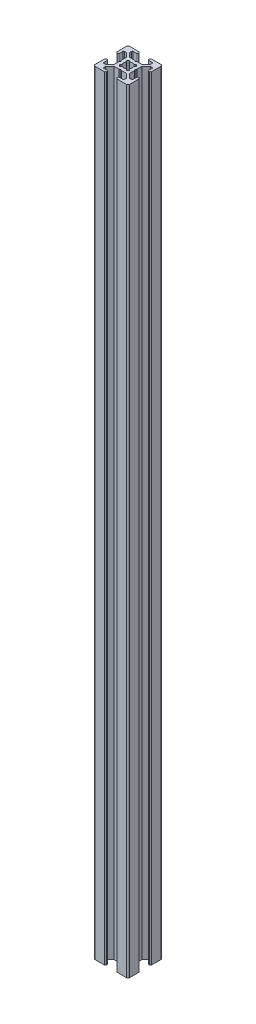
SolidWorks part; units mm, degrees
ref_plane "Front Plane" through (0, 0, 0) normal (0, 0, 1) x (1, 0, 0)
ref_plane "Top Plane" through (0, 0, 0) normal (0, 1, 0) x (1, 0, 0)
ref_plane "Right Plane" through (0, 0, 0) normal (1, 0, 0) x (0, 0, -1)
sketch "Sketch3" plane through (0, 0, 0) normal (0, 1, 0) x (1, 0, 0)
  line L0 (7, 20) -> (7, 18.5)
  line L1 (0, 0) -> (20, 0)
  line L2 (0, 0) -> (0, 20)
  line L3 (0, 20) -> (20, 20)
  line L4 (20, 0) -> (20, 20)
  line L5 (7, 18.5) -> (4, 18.5)
  line L6 (4, 18.5) -> (4, 17)
  line L7 (4, 17) -> (6.5, 14.5)
  line L8 (6.5, 14.5) -> (13.5, 14.5)
  line L9 (13.5, 14.5) -> (16, 17)
  line L10 (16, 17) -> (16, 18.5)
  line L11 (16, 18.5) -> (13, 18.5)
  line L12 (13, 18.5) -> (13, 20)
  line L13 (13, 20) -> (7, 20)
  line L14 (9.5, 14.5) -> (10, 14)
  line L15 (10, 14) -> (10.5, 14.5)
  line L16 (10.5, 14.5) -> (9.5, 14.5)
  line L17 (13, 19.5) -> (13, 20)
  line L18 (13.5, 20) -> (13, 20)
  line L19 (7, 19.5) -> (7, 20)
  line L20 (6.5, 20) -> (7, 20)
  line L21 (0, 13) -> (1.5, 13)
  line L22 (1.5, 13) -> (1.5, 16)
  line L23 (1.5, 16) -> (3, 16)
  line L24 (3, 16) -> (5.5, 13.5)
  line L25 (5.5, 13.5) -> (5.5, 6.5)
  line L26 (5.5, 6.5) -> (3, 4)
  line L27 (3, 4) -> (1.5, 4)
  line L28 (1.5, 4) -> (1.5, 7)
  line L29 (1.5, 7) -> (0, 7)
  line L30 (0, 7) -> (0, 13)
  line L31 (5.5, 10.5) -> (5.5, 9.5)
  line L32 (5.5, 9.5) -> (6, 10)
  line L33 (6, 10) -> (5.5, 10.5)
  line L34 (0.5, 13) -> (0, 13)
  line L35 (0, 13.5) -> (0, 13)
  line L36 (0, 6.5) -> (0, 7)
  line L37 (0.5, 7) -> (0, 7)
  line L38 (10, 20) -> (10, 0) construction
  line L39 (20, 10) -> (0, 10) construction
  line L40 (10, 6) -> (10.5, 5.5)
  line L41 (9.5, 5.5) -> (10, 6)
  line L42 (10.5, 5.5) -> (9.5, 5.5)
  line L43 (13.5, 0) -> (13, 0)
  line L44 (13, 0.5) -> (13, 0)
  line L45 (6.5, 0) -> (7, 0)
  line L46 (7, 0.5) -> (7, 0)
  line L47 (13, 1.5) -> (13, 0)
  line L48 (16, 1.5) -> (13, 1.5)
  line L49 (16, 3) -> (16, 1.5)
  line L50 (13.5, 5.5) -> (16, 3)
  line L51 (6.5, 5.5) -> (13.5, 5.5)
  line L52 (4, 3) -> (6.5, 5.5)
  line L53 (4, 1.5) -> (4, 3)
  line L54 (7, 1.5) -> (4, 1.5)
  line L55 (7, 0) -> (7, 1.5)
  line L56 (13, 0) -> (7, 0)
  line L57 (14.5, 9.5) -> (14, 10)
  line L58 (14.5, 10.5) -> (14.5, 9.5)
  line L59 (14, 10) -> (14.5, 10.5)
  line L60 (19.5, 7) -> (20, 7)
  line L61 (20, 6.5) -> (20, 7)
  line L62 (20, 13.5) -> (20, 13)
  line L63 (19.5, 13) -> (20, 13)
  line L64 (18.5, 7) -> (20, 7)
  line L65 (18.5, 4) -> (18.5, 7)
  line L66 (17, 4) -> (18.5, 4)
  line L67 (14.5, 6.5) -> (17, 4)
  line L68 (14.5, 13.5) -> (14.5, 6.5)
  line L69 (17, 16) -> (14.5, 13.5)
  line L70 (18.5, 16) -> (17, 16)
  line L71 (18.5, 13) -> (18.5, 16)
  line L72 (20, 13) -> (18.5, 13)
  line L73 (20, 7) -> (20, 13)
  arc A0 (13.5, 20) -> (13, 19.5) centre (13, 20) cw
  arc A1 (6.5, 20) -> (7, 19.5) centre (7, 20) ccw
  arc A2 (0.5, 13) -> (0, 13.5) centre (0, 13) ccw
  arc A3 (0.5, 7) -> (0, 6.5) centre (0, 7) cw
  arc A4 (13.5, 0) -> (13, 0.5) centre (13, 0) ccw
  arc A5 (6.5, 0) -> (7, 0.5) centre (7, 0) cw
  arc A6 (19.5, 7) -> (20, 6.5) centre (20, 7) ccw
  arc A7 (19.5, 13) -> (20, 13.5) centre (20, 13) cw
  point P7 (10, 14.5)
  point P16 (10, 20)
  point P26 (5.5, 10)
  point P35 (0, 10)
  dimension "D16" = 0.5
  dimension "D17" = 0.5
  dimension "D28" = 0.5
  dimension "D29" = 0.5
  dimension "D1" = 20
  dimension "D2" = 20
  dimension "D3" = 7
  dimension "D4" = 7
  dimension "D5" = 1.5
  dimension "D6" = 1.5
  dimension "D7" = 3
  dimension "D8" = 3
  dimension "D9" = 1.5
  dimension "D10" = 1.5
  dimension "D11" = 7
  dimension "D12" = 5.5
  dimension "D13" = 0.5
  dimension "D14" = 0.5
  dimension "D15" = 0.5
  dimension "D18" = 7
  dimension "D19" = 7
  dimension "D20" = 1.5
  dimension "D21" = 1.5
  dimension "D22" = 3
  dimension "D23" = 7
  dimension "D24" = 5.5
  dimension "D25" = 0.5
  dimension "D26" = 0.5
  dimension "D27" = 0.5
extrude "Boss-Extrude1" add sketch "Sketch3" along normal blind 448 contours L72 A7 L4 L3 A0 L12 L11 L10 L9 L8 L15 L14 L7 L6 L5 L0 A1 L2 A2 L21 L22 L23 L24 L25 L33 L32 L26 L27 L28 L29 A3 L1 A5 L55 L54 L53 L52 L51 L41 L40 L50 L49 L48 L47 A4
fillet "Fillet1" radius 1 4 edges at (0, 224, 0) (20, 224, 0) (20, 224, -20) (0, 224, -20)
sketch "Sketch4" plane through (0, 448, 0) normal (0, 1, 0) x (1, 0, 0)
  line L0 (13.5, 14.5) -> (5.5, 6.5) construction
  line L1 (14.5, 13.5) -> (6.5, 5.5) construction
  line L2 (10.5, 14.5) -> (14.5, 10.5) construction
  line L3 (12, 13) -> (13, 12)
  line L4 (13, 12) -> (8, 7)
  line L5 (8, 7) -> (7, 8)
  line L6 (7, 8) -> (12, 13)
  line L7 (13.5, 14.5) -> (16, 17) construction
  line L8 (17, 16) -> (14.5, 13.5) construction
  line L9 (5.5, 9.5) -> (9.5, 5.5) construction
  line L10 (5.5, 10.5) -> (9.5, 14.5) construction
  line L11 (14.5, 9.5) -> (10.5, 5.5) construction
  line L12 (6.5, 14.5) -> (14.5, 6.5) construction
  line L13 (5.5, 13.5) -> (13.5, 5.5) construction
  line L14 (7, 12) -> (8, 13)
  line L15 (8, 13) -> (13, 8)
  line L16 (13, 8) -> (12, 7)
  line L17 (12, 7) -> (7, 12)
  line L18 (4, 17) -> (6.5, 14.5) construction
  line L19 (3, 16) -> (5.5, 13.5) construction
  line L20 (20, 10) -> (0, 10) construction
  circle A0 centre (10, 10) radius 2.5
  dimension "D1" = 5
extrude "Cut-Extrude1" cut sketch "Sketch4" against normal through all contours L6 A0 L15 | L4 A0 L6 L15 | L15 A0 L17 L6 | L17 L4 L15 L6 | L17 A0 L6 | L6 A0 L4 L17 | L4 A0 L17 | L17 A0 L15 L4 | L15 A0 L4 | A0 L6 L5 L4 | A0 L17 L16 L15 | A0 L4 L3 L6 | A0 L15 L14 L17
fillet "Fillet2" radius 0.5 24 edges at (1.5, 224, -16) (1.5, 224, -13) (5.5, 224, -10.5) (5.5, 224, -9.5) (1.5, 224, -7) (1.5, 224, -4) (4, 224, -1.5) (7, 224, -1.5) (9.5, 224, -5.5) (10.5, 224, -5.5) (13, 224, -1.5) (16, 224, -1.5) (18.5, 224, -4) (18.5, 224, -7) (18.5, 224, -13) (18.5, 224, -16) (14.5, 224, -9.5) (14.5, 224, -10.5) (10.5, 224, -14.5) (9.5, 224, -14.5) (16, 224, -18.5) (13, 224, -18.5) (7, 224, -18.5) (4, 224, -18.5)
fillet "Fillet3" radius 0.25 8 edges at (13, 224, -8) (12, 224, -7) (13, 224, -12) (12, 224, -13) (8, 224, -13) (7, 224, -12) (7, 224, -8) (8, 224, -7)
